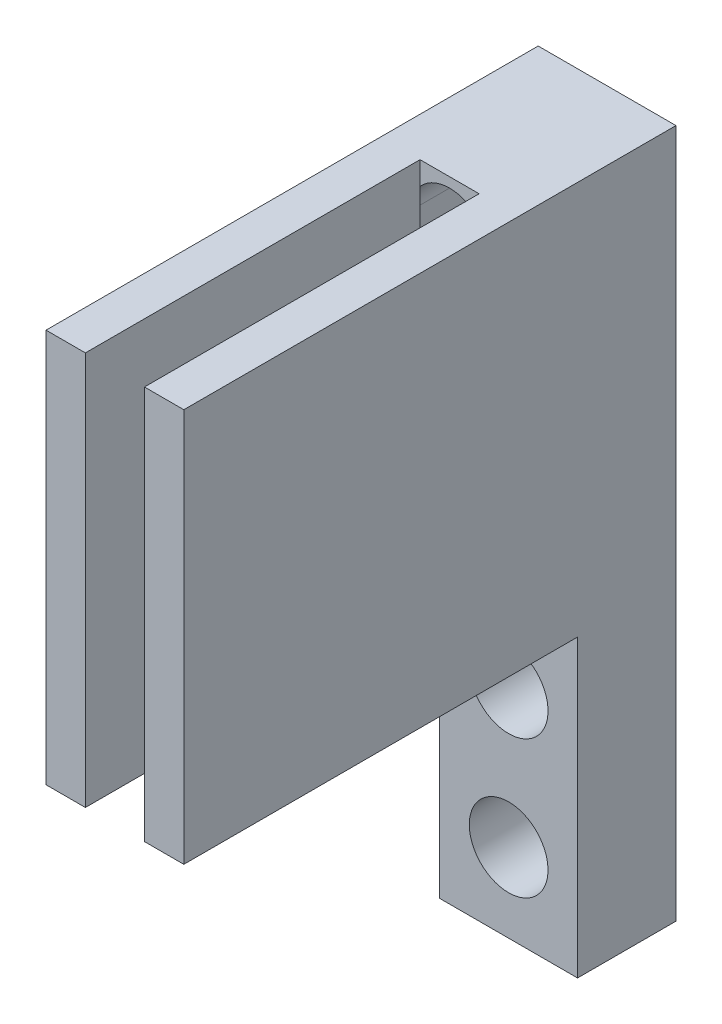
SolidWorks part; units mm, degrees
ref_plane "Front Plane" through (0, 0, 0) normal (0, 0, 1) x (1, 0, 0)
ref_plane "Top Plane" through (0, 0, 0) normal (0, 1, 0) x (1, 0, 0)
ref_plane "Right Plane" through (0, 0, 0) normal (1, 0, 0) x (0, 0, -1)
sketch "Sketch1" plane through (0, 0, 0) normal (0, 1, 0) x (1, 0, 0)
  line L0 (-1.5, -12.5) -> (-1.5, 4.5)
  line L5 (3.5, -12.5) -> (1.5, -12.5)
  line L6 (3.5, -12.5) -> (3.5, 12.5)
  line L11 (3.5, 12.5) -> (-3.5, 12.5)
  line L12 (-3.5, -12.5) -> (-3.5, 12.5)
  line L13 (3.5, -12.5) -> (-3.5, 12.5) construction
  line L14 (3.5, 12.5) -> (-3.5, -12.5) construction
  line L15 (-1.5, 4.5) -> (1.5, 4.5)
  line L16 (1.5, 4.5) -> (1.5, -12.5)
  line L17 (-1.5, -12.5) -> (-3.5, -12.5)
  line L18 (-1.5, -12.5) -> (1.5, -12.5) construction
  point P0 (0, 0)
  point P8 (3.5, -5.115)
  dimension "D1" = 2
  dimension "D2" = 3
  dimension "D3" = 8
  dimension "D4" = 25
extrude "Boss-Extrude1" add sketch "Sketch1" along normal blind 20
sketch "Sketch2" plane through (0, 0, -4.5) normal (0, 0, 1) x (1, 0, 0)
  line L0 (0, 17.5) -> (0, 10.5) construction
  line L1 (2, 17.5) -> (2, 10.5)
  line L2 (-2, 17.5) -> (-2, 10.5)
  line L3 (-1.5, 20) -> (1.5, 20) construction
  arc A0 (2, 17.5) -> (-2, 17.5) centre (0, 17.5) ccw
  arc A1 (-2, 10.5) -> (2, 10.5) centre (0, 10.5) ccw
  point P3 (0, 14)
  point P10 (0, 20)
  point P11 (0, 0)
  dimension "D3" = 2
  dimension "D1" = 7
  dimension "D2" = 6
extrude "Cut-Extrude3" cut sketch "Sketch2" against normal up to surface (8 mm away) up to face at (0, 10, -12.5)
sketch "Sketch4" plane through (0, 0, -12.5) normal (0, 0, -1) x (-1, 0, 0)
  line L1 (-3.5, 0) -> (3.5, 0)
  line L2 (-3.5, 0) -> (-3.5, -15)
  line L3 (-3.5, -15) -> (3.5, -15)
  line L4 (3.5, 0) -> (3.5, -15)
  line L5 (3.5, 20) -> (3.5, 0) construction
  line L6 (0, -15) -> (0, 0) construction
  circle A0 centre (0, -4) radius 2
  circle A1 centre (0, -11) radius 2
  point P11 (0, 0)
  point P14 (0, 0)
  point P15 (0, -7.3745)
  point P16 (0, -2.7307)
  dimension "D2" = 4
  dimension "D1" = 15
  dimension "D3" = 4
  dimension "D4" = 4
extrude "Boss-Extrude2" add sketch "Sketch4" against normal blind 5
